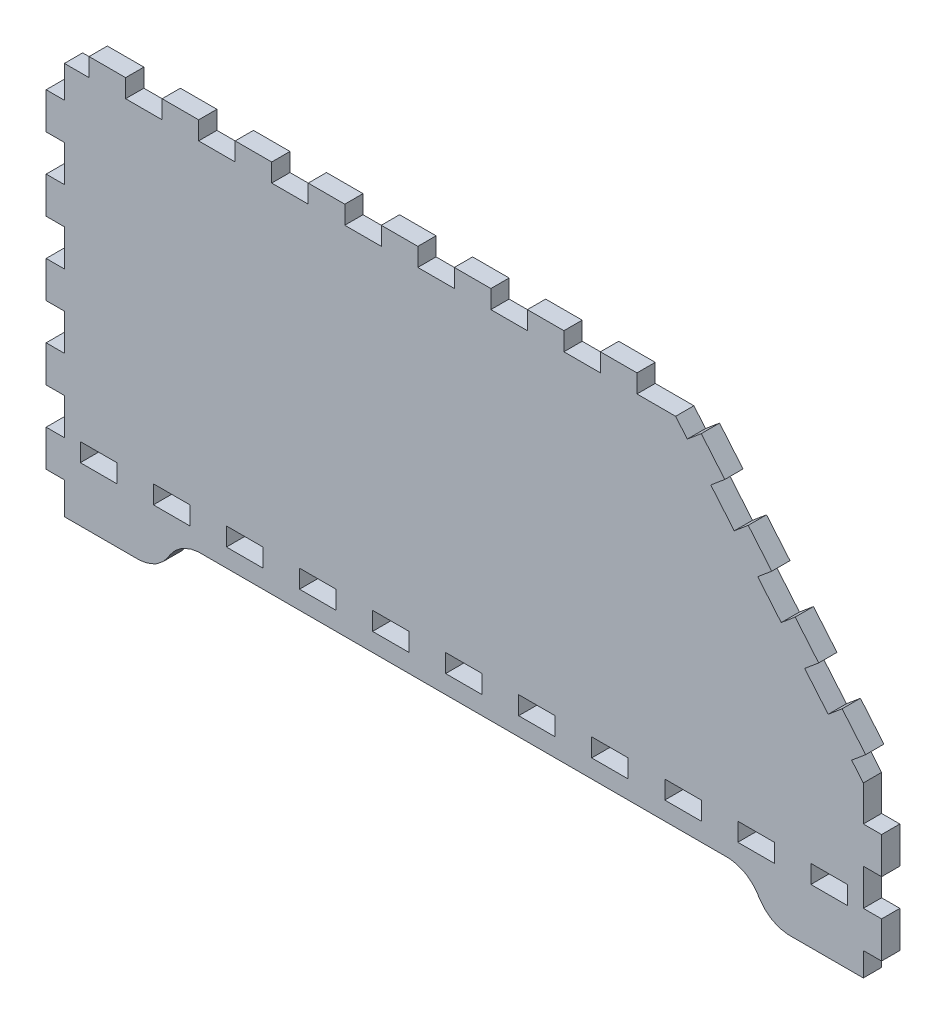
SolidWorks part; units mm, degrees
material "Acrylic (Medium-high impact)"
ref_plane "Front Plane" through (0, 0, 0) normal (0, 0, 1) x (1, 0, 0)
ref_plane "Top Plane" through (0, 0, 0) normal (0, 1, 0) x (1, 0, 0)
ref_plane "Right Plane" through (0, 0, 0) normal (1, 0, 0) x (0, 0, -1)
sketch "Model" plane through (0, 0, 0) normal (0, 0, 1) x (1, 0, 0)
  line L4 (26.8153, 40.3461) -> (21.1005, 40.3461)
  line L5 (21.1005, 40.3461) -> (21.1005, 46.0609)
  line L6 (21.1005, 46.0609) -> (32.53, 46.0609)
  line L7 (32.53, 46.0609) -> (32.53, 40.3461)
  line L8 (32.53, 40.3461) -> (26.8153, 40.3461)
  line L9 (49.6758, 40.3461) -> (43.9593, 40.3461)
  line L10 (43.9593, 40.3461) -> (43.9593, 46.0609)
  line L11 (43.9593, 46.0609) -> (55.3903, 46.0609)
  line L12 (55.3903, 46.0609) -> (55.3903, 40.3461)
  line L13 (55.3903, 40.3461) -> (49.6758, 40.3461)
  line L14 (72.5343, 40.3461) -> (66.8195, 40.3461)
  line L15 (66.8195, 40.3461) -> (66.8195, 46.0609)
  line L16 (66.8195, 46.0609) -> (78.2508, 46.0609)
  line L17 (78.2508, 46.0609) -> (78.2508, 40.3461)
  line L18 (78.2508, 40.3461) -> (72.5343, 40.3461)
  line L19 (95.3945, 40.3461) -> (89.68, 40.3461)
  line L20 (89.68, 40.3461) -> (89.68, 46.0609)
  line L21 (89.68, 46.0609) -> (101.1093, 46.0609)
  line L22 (101.1093, 46.0609) -> (101.1093, 40.3461)
  line L23 (101.1093, 40.3461) -> (95.3945, 40.3461)
  line L24 (118.255, 40.3461) -> (112.5403, 40.3461)
  line L25 (112.5403, 40.3461) -> (112.5403, 46.0609)
  line L26 (112.5403, 46.0609) -> (123.9695, 46.0609)
  line L27 (123.9695, 46.0609) -> (123.9695, 40.3461)
  line L28 (123.9695, 40.3461) -> (118.255, 40.3461)
  line L29 (141.1153, 40.3461) -> (135.4008, 40.3461)
  line L30 (135.4008, 40.3461) -> (135.4008, 46.0609)
  line L31 (135.4008, 46.0609) -> (146.83, 46.0609)
  line L32 (146.83, 46.0609) -> (146.83, 40.3461)
  line L33 (146.83, 40.3461) -> (141.1153, 40.3461)
  line L34 (163.9758, 40.3461) -> (158.2593, 40.3461)
  line L35 (158.2593, 40.3461) -> (158.2593, 46.0609)
  line L36 (158.2593, 46.0609) -> (169.6903, 46.0609)
  line L37 (169.6903, 46.0609) -> (169.6903, 40.3461)
  line L38 (169.6903, 40.3461) -> (163.9758, 40.3461)
  line L39 (186.8343, 40.3461) -> (181.1195, 40.3461)
  line L40 (181.1195, 40.3461) -> (181.1195, 46.0609)
  line L41 (181.1195, 46.0609) -> (192.5508, 46.0609)
  line L42 (192.5508, 46.0609) -> (192.5508, 40.3461)
  line L43 (192.5508, 40.3461) -> (186.8343, 40.3461)
  line L44 (209.6945, 40.3461) -> (203.98, 40.3461)
  line L45 (203.98, 40.3461) -> (203.98, 46.0609)
  line L46 (203.98, 46.0609) -> (215.4093, 46.0609)
  line L47 (215.4093, 46.0609) -> (215.4093, 40.3461)
  line L48 (215.4093, 40.3461) -> (209.6945, 40.3461)
  line L49 (232.555, 40.3461) -> (226.8403, 40.3461)
  line L50 (226.8403, 40.3461) -> (226.8403, 46.0609)
  line L51 (226.8403, 46.0609) -> (238.2695, 46.0609)
  line L52 (238.2695, 46.0609) -> (238.2695, 40.3461)
  line L53 (238.2695, 40.3461) -> (232.555, 40.3461)
  line L54 (255.4148, 40.3461) -> (249.7008, 40.3461)
  line L55 (249.7008, 40.3461) -> (249.7008, 46.0609)
  line L56 (249.7008, 46.0609) -> (261.1298, 46.0609)
  line L57 (261.1298, 46.0609) -> (261.1298, 40.3461)
  line L58 (261.1298, 40.3461) -> (255.4148, 40.3461)
  line L59 (16.1148, 23.2006) -> (38.9748, 23.2006)
  line L60 (38.9748, 23.2006) -> (39.7137, 23.2006)
  line L61 (39.7137, 23.2006) -> (41.9321, 23.5906)
  line L62 (41.9321, 23.5906) -> (44.2542, 24.4809)
  line L63 (44.2542, 24.4809) -> (44.6898, 24.7316)
  line L64 (44.6898, 24.7316) -> (45.1239, 24.9838)
  line L65 (45.1239, 24.9838) -> (47.056, 26.5494)
  line L66 (47.056, 26.5494) -> (48.6227, 28.4813)
  line L67 (48.6227, 28.4813) -> (48.8734, 28.9154)
  line L68 (48.8734, 28.9154) -> (49.1244, 29.3507)
  line L69 (49.1244, 29.3507) -> (50.69, 31.2829)
  line L70 (50.69, 31.2829) -> (52.6217, 32.8483)
  line L71 (52.6217, 32.8483) -> (53.057, 33.099)
  line L72 (53.057, 33.099) -> (53.4914, 33.3499)
  line L73 (53.4914, 33.3499) -> (55.8132, 34.2415)
  line L74 (55.8132, 34.2415) -> (58.0319, 34.6301)
  line L75 (58.0319, 34.6301) -> (58.772, 34.6301)
  line L76 (58.772, 34.6301) -> (223.4585, 34.6301)
  line L77 (223.4585, 34.6301) -> (224.1974, 34.6301)
  line L78 (224.1974, 34.6301) -> (226.4159, 34.2415)
  line L79 (226.4159, 34.2415) -> (228.7379, 33.3499)
  line L80 (228.7379, 33.3499) -> (229.1733, 33.099)
  line L81 (229.1733, 33.099) -> (229.6071, 32.8483)
  line L82 (229.6071, 32.8483) -> (231.5393, 31.2829)
  line L83 (231.5393, 31.2829) -> (233.1049, 29.3507)
  line L84 (233.1049, 29.3507) -> (233.3554, 28.9154)
  line L85 (233.3554, 28.9154) -> (233.6063, 28.4813)
  line L86 (233.6063, 28.4813) -> (235.172, 26.5494)
  line L87 (235.172, 26.5494) -> (237.1037, 24.9838)
  line L88 (237.1037, 24.9838) -> (237.5393, 24.7316)
  line L89 (237.5393, 24.7316) -> (237.9734, 24.4809)
  line L90 (237.9734, 24.4809) -> (240.2967, 23.5906)
  line L91 (240.2967, 23.5906) -> (242.5154, 23.2006)
  line L92 (242.5154, 23.2006) -> (243.2555, 23.2006)
  line L93 (243.2555, 23.2006) -> (266.1133, 23.2006)
  line L94 (266.1133, 23.2006) -> (266.1133, 30.6489)
  line L95 (266.1133, 30.6489) -> (271.8308, 30.6489)
  line L96 (271.8308, 30.6489) -> (271.8308, 42.0784)
  line L97 (271.8308, 42.0784) -> (266.1133, 42.0784)
  line L98 (266.1133, 42.0784) -> (266.1133, 53.5094)
  line L99 (266.1133, 53.5094) -> (271.8308, 53.5094)
  line L100 (271.8308, 53.5094) -> (271.8308, 64.9387)
  line L101 (271.8308, 64.9387) -> (266.1133, 64.9387)
  line L102 (266.1133, 64.9387) -> (266.1133, 76.0606)
  line L103 (266.1133, 76.0606) -> (262.4607, 80.4139)
  line L104 (262.4607, 80.4139) -> (266.8397, 84.0877)
  line L105 (266.8397, 84.0877) -> (259.4915, 92.8441)
  line L106 (259.4915, 92.8441) -> (255.1125, 89.1703)
  line L107 (255.1125, 89.1703) -> (247.7671, 97.9261)
  line L108 (247.7671, 97.9261) -> (252.145, 101.6)
  line L109 (252.145, 101.6) -> (244.7973, 110.3559)
  line L110 (244.7973, 110.3559) -> (240.4194, 106.682)
  line L111 (240.4194, 106.682) -> (233.0732, 115.4384)
  line L112 (233.0732, 115.4384) -> (237.4511, 119.1123)
  line L113 (237.4511, 119.1123) -> (230.1034, 127.8682)
  line L114 (230.1034, 127.8682) -> (225.7255, 124.1943)
  line L115 (225.7255, 124.1943) -> (218.379, 132.9502)
  line L116 (218.379, 132.9502) -> (222.7572, 136.6241)
  line L117 (222.7572, 136.6241) -> (215.4093, 145.3789)
  line L118 (215.4093, 145.3789) -> (211.0313, 141.7066)
  line L119 (211.0313, 141.7066) -> (207.3783, 146.0609)
  line L120 (207.3783, 146.0609) -> (195.2833, 146.0609)
  line L121 (195.2833, 146.0609) -> (195.2833, 151.7757)
  line L122 (195.2833, 151.7757) -> (183.8523, 151.7757)
  line L123 (183.8523, 151.7757) -> (183.8523, 146.0609)
  line L124 (183.8523, 146.0609) -> (172.4231, 146.0609)
  line L125 (172.4231, 146.0609) -> (172.4231, 151.7757)
  line L126 (172.4231, 151.7757) -> (160.9933, 151.7757)
  line L127 (160.9933, 151.7757) -> (160.9933, 146.0609)
  line L128 (160.9933, 146.0609) -> (149.5626, 146.0609)
  line L129 (149.5626, 146.0609) -> (149.5626, 151.7757)
  line L130 (149.5626, 151.7757) -> (138.1333, 151.7757)
  line L131 (138.1333, 151.7757) -> (138.1333, 146.0609)
  line L132 (138.1333, 146.0609) -> (126.7023, 146.0609)
  line L133 (126.7023, 146.0609) -> (126.7023, 151.7757)
  line L134 (126.7023, 151.7757) -> (115.2731, 151.7757)
  line L135 (115.2731, 151.7757) -> (115.2731, 146.0609)
  line L136 (115.2731, 146.0609) -> (103.8433, 146.0609)
  line L137 (103.8433, 146.0609) -> (103.8433, 151.7757)
  line L138 (103.8433, 151.7757) -> (92.4126, 151.7757)
  line L139 (92.4126, 151.7757) -> (92.4126, 146.0609)
  line L140 (92.4126, 146.0609) -> (80.9833, 146.0609)
  line L141 (80.9833, 146.0609) -> (80.9833, 151.7757)
  line L142 (80.9833, 151.7757) -> (69.5523, 151.7757)
  line L143 (69.5523, 151.7757) -> (69.5523, 146.0609)
  line L144 (69.5523, 146.0609) -> (58.1231, 146.0609)
  line L145 (58.1231, 146.0609) -> (58.1231, 151.7757)
  line L146 (58.1231, 151.7757) -> (46.6933, 151.7757)
  line L147 (46.6933, 151.7757) -> (46.6933, 146.0609)
  line L148 (46.6933, 146.0609) -> (35.2626, 146.0609)
  line L149 (35.2626, 146.0609) -> (35.2626, 151.7757)
  line L150 (35.2626, 151.7757) -> (23.8332, 151.7757)
  line L151 (23.8332, 151.7757) -> (23.8332, 146.0609)
  line L152 (23.8332, 146.0609) -> (16.1148, 146.0609)
  line L153 (16.1148, 146.0609) -> (16.1148, 136.066)
  line L154 (16.1148, 136.066) -> (10.4001, 136.066)
  line L155 (10.4001, 136.066) -> (10.4001, 124.6353)
  line L156 (10.4001, 124.6353) -> (16.1148, 124.6353)
  line L157 (16.1148, 124.6353) -> (16.1148, 113.2058)
  line L158 (16.1148, 113.2058) -> (10.4001, 113.2058)
  line L159 (10.4001, 113.2058) -> (10.4001, 101.775)
  line L160 (10.4001, 101.775) -> (16.1148, 101.775)
  line L161 (16.1148, 101.775) -> (16.1148, 90.3458)
  line L162 (16.1148, 90.3458) -> (10.4001, 90.3458)
  line L163 (10.4001, 90.3458) -> (10.4001, 78.916)
  line L164 (10.4001, 78.916) -> (16.1148, 78.916)
  line L165 (16.1148, 78.916) -> (16.1148, 67.4853)
  line L166 (16.1148, 67.4853) -> (10.4001, 67.4853)
  line L167 (10.4001, 67.4853) -> (10.4001, 56.0558)
  line L168 (10.4001, 56.0558) -> (16.1148, 56.0558)
  line L169 (16.1148, 56.0558) -> (16.1148, 44.625)
  line L170 (16.1148, 44.625) -> (10.4001, 44.625)
  line L171 (10.4001, 44.625) -> (10.4001, 33.1955)
  line L172 (10.4001, 33.1955) -> (16.1148, 33.1955)
  line L173 (16.1148, 33.1955) -> (16.1148, 23.2006)
extrude "Boss-Extrude1" add sketch "Model" along normal blind 5.715
